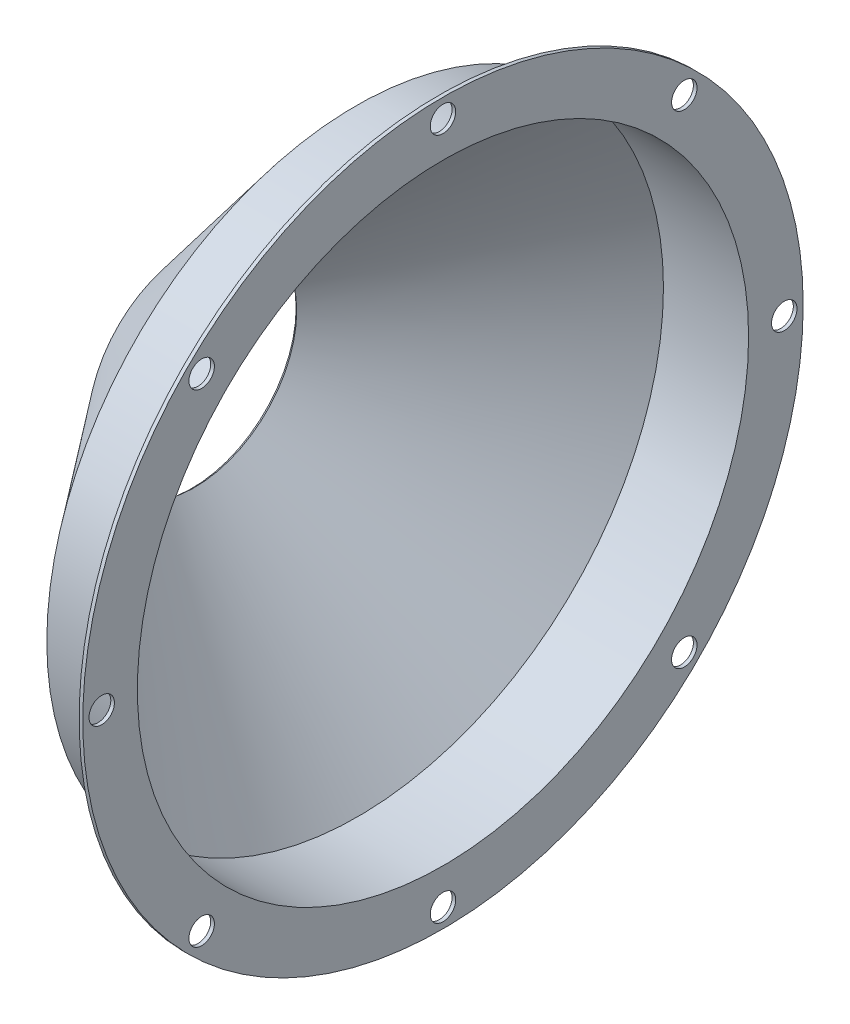
SolidWorks part; units mm, degrees
ref_plane "Front Plane" through (0, 0, 0) normal (0, 0, 1) x (1, 0, 0)
ref_plane "Top Plane" through (0, 0, 0) normal (0, 1, 0) x (1, 0, 0)
ref_plane "Right Plane" through (0, 0, 0) normal (1, 0, 0) x (0, 0, -1)
sketch "Sketch1" plane through (0, 0, 0) normal (0, 0, 1) x (1, 0, 0)
  line L0 (0, 0) -> (-1101.2129, 0) construction
  line L1 (-1101.2129, 25.4) -> (-1060.5729, 76.2)
  line L2 (-1060.5729, 76.2) -> (-1040.2529, 76.2)
  line L3 (-1101.9249, 25.9696) -> (-1061.0112, 77.1119)
  line L4 (-1061.0112, 77.1119) -> (-1040.2529, 77.1119)
  line L5 (-1101.9249, 25.9696) -> (-1101.2129, 25.4)
  line L7 (-1040.2529, 77.1119) -> (-1040.2529, 89.8119)
  line L8 (-1040.2529, 89.8119) -> (-1039.341, 89.8119)
  line L9 (-1039.341, 89.8119) -> (-1039.341, 76.2)
  line L10 (-1039.341, 76.2) -> (-1040.2529, 76.2)
  dimension "D1" = 25.4
  dimension "D2" = 76.2
  dimension "D3" = 40.64
  dimension "D4" = 20.32
  dimension "D5" = 0.9119
  dimension "D6" = 0.9119
  dimension "D7" = 12.7
revolve "Revolve1" add sketch "Sketch1" angle 360 about L0
sketch "Sketch3" plane through (-1040.2529, 0, 0) normal (-1, 0, 0) x (0, 0, 1)
  circle A0 centre (0, 85.09) radius 3.175
  dimension "D1" = 6.35
  dimension "D2" = 85.09
extrude "Cut-Extrude1" cut sketch "Sketch3" against normal up to surface (0.9119 mm away) from surface at 0 up to face at (-1039.341, 0, -89.8119) starting at face at (-1040.2529, 0, -77.1119)
pattern_circular "CirPattern1" count 8 over 360 about axis through (0, 0, 0) along (1, 0, 0) of "Cut-Extrude1"
